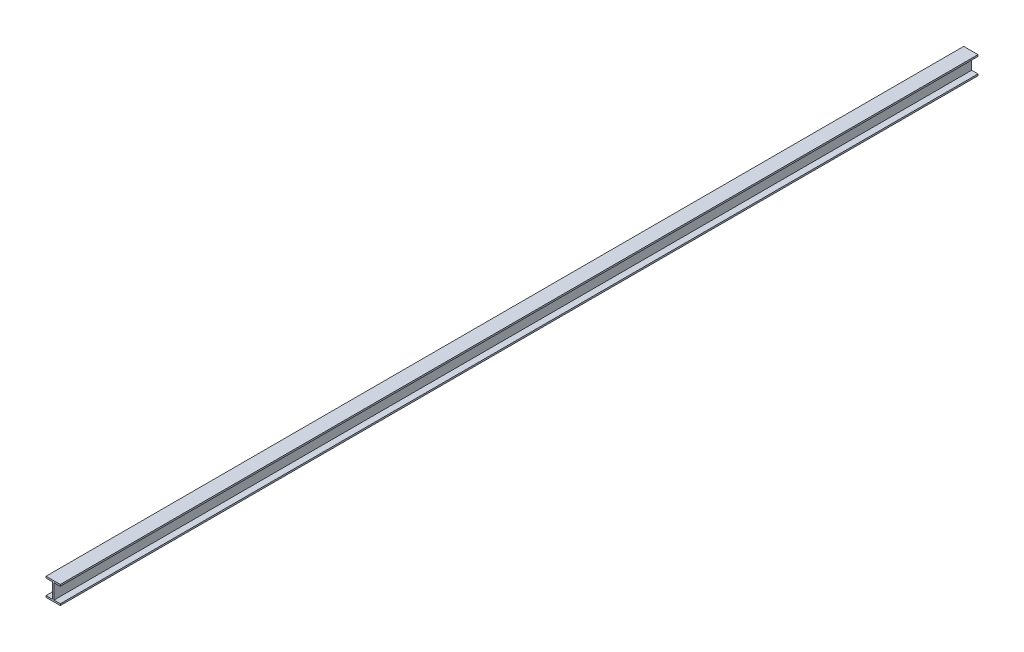
SolidWorks part; units mm, degrees
ref_plane "Front Plane" through (0, 0, 0) normal (0, 0, 1) x (1, 0, 0)
ref_plane "Top Plane" through (0, 0, 0) normal (0, 1, 0) x (1, 0, 0)
ref_plane "Right Plane" through (0, 0, 0) normal (1, 0, 0) x (0, 0, -1)
sketch "Sketch1" plane through (0, 0, 0) normal (0, 0, 1) x (1, 0, 0)
  line L0 (156, -32) -> (280, -32)
  line L1 (0, 0) -> (280, 0)
  line L2 (0, 0) -> (0, -32)
  line L3 (0, -360) -> (280, -360)
  line L4 (280, 0) -> (280, -32)
  line L5 (124, 0) -> (156, 0)
  line L6 (124, -32) -> (124, -328)
  line L7 (124, -360) -> (156, -360)
  line L8 (156, -32) -> (156, -328)
  line L9 (0, 0) -> (280, 0)
  line L10 (0, 0) -> (0, -32)
  line L11 (0, -32) -> (124, -32)
  line L12 (280, 0) -> (280, -32)
  line L13 (0, -360) -> (280, -360)
  line L14 (0, -360) -> (0, -328)
  line L15 (0, -328) -> (124, -328)
  line L16 (280, -360) -> (280, -328)
  line L17 (0, -328) -> (0, -360)
  line L18 (280, -328) -> (280, -360)
  line L19 (156, -328) -> (280, -328)
  dimension "D1" = 280
  dimension "D2" = 360
  dimension "D3" = 32
  dimension "D4" = 32
  dimension "D5" = 124
  dimension "D6" = 124
extrude "Boss-Extrude1" add sketch "Sketch1" along normal blind 18000 contours L19 L8 L0 L4 L1 L2 L11 L6 L15 L14 L3 L16
